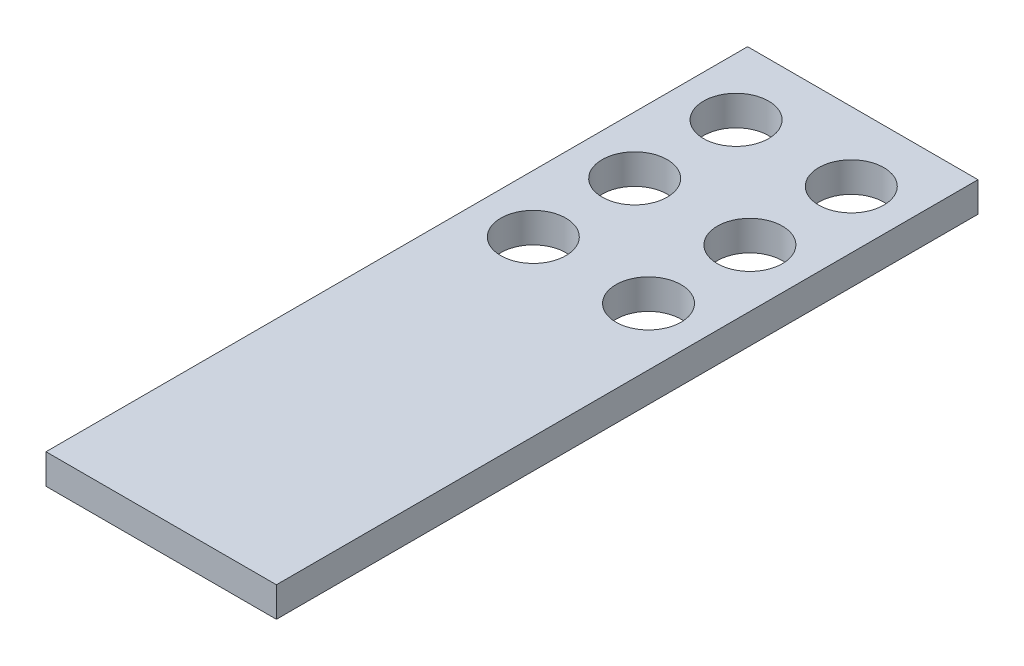
SolidWorks part; units mm, degrees
ref_plane "Front Plane" through (0, 0, 0) normal (0, 0, 1) x (1, 0, 0)
ref_plane "Top Plane" through (0, 0, 0) normal (0, 1, 0) x (1, 0, 0)
ref_plane "Right Plane" through (0, 0, 0) normal (1, 0, 0) x (0, 0, -1)
sketch "Sketch1" plane through (0, 0, 0) normal (0, 1, 0) x (1, 0, 0)
  line L0 (50, -60) -> (150, -60) construction
  line L1 (0, 0) -> (200, 0)
  line L2 (0, 0) -> (0, -609)
  line L3 (0, -609) -> (200, -609)
  line L4 (200, 0) -> (200, -609)
  line L7 (0, -88) -> (0, -697) [skipped]
  line L8 (0, -176) -> (0, -785) [skipped]
  circle A0 centre (50, -60) radius 28.25
  circle A1 centre (150, -60) radius 28.25
  circle A2 centre (50, -148) radius 28.25
  circle A3 centre (150, -148) radius 28.25
  circle A4 centre (50, -236) radius 28.25
  circle A5 centre (150, -236) radius 28.25
  point P5 (100, -60)
  point P9 (100, 0)
  point P11 (0, 0)
  dimension "D3" = 28.25
  dimension "D1" = 609
  dimension "D2" = 200
  dimension "D4" = 60
  dimension "D5" = 100
  dimension "D7" = 88
  dimension "D6" = 3
extrude "Boss-Extrude1" add sketch "Sketch1" along normal blind 26
